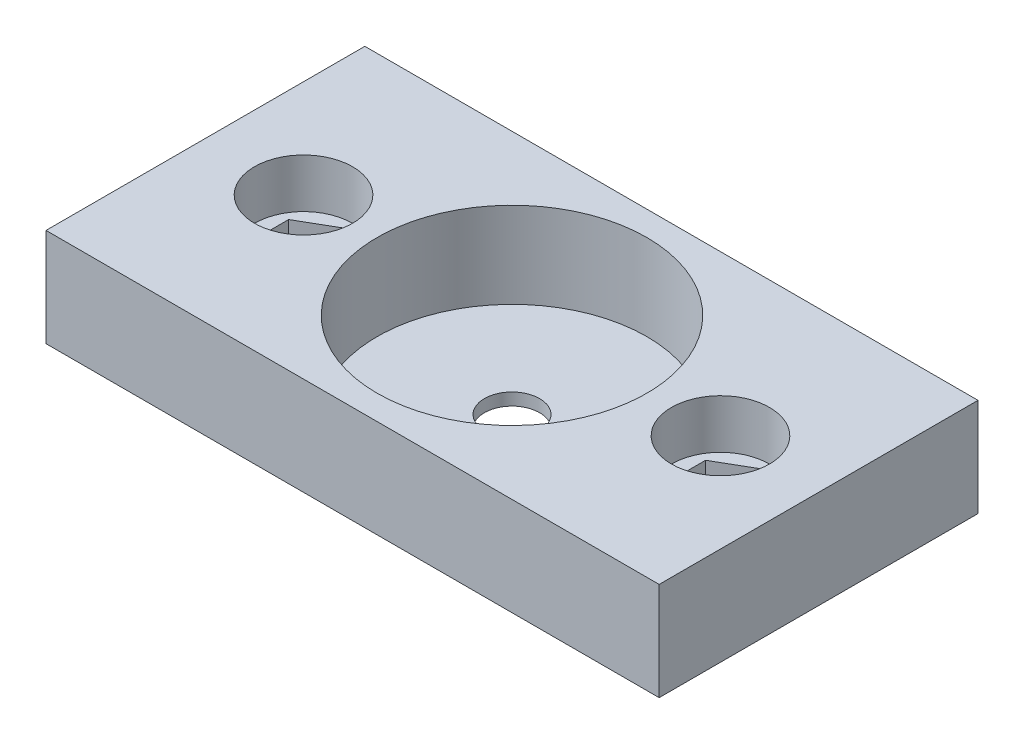
SolidWorks part; units mm, degrees
ref_plane "Front Plane" through (0, 0, 0) normal (0, 0, 1) x (1, 0, 0)
ref_plane "Top Plane" through (0, 0, 0) normal (0, 1, 0) x (1, 0, 0)
ref_plane "Right Plane" through (0, 0, 0) normal (1, 0, 0) x (0, 0, -1)
sketch "Sketch1" plane through (0, 0, 0) normal (0, 1, 0) x (1, 0, 0)
  line L1 (-25, 13) -> (25, 13)
  line L2 (-25, 13) -> (-25, -13)
  line L3 (-25, -13) -> (25, -13)
  line L4 (25, 13) -> (25, -13)
  line L5 (0, -13) -> (0, 13) construction
  line L6 (-25, 0) -> (25, 0) construction
  point P4 (0, 0)
  point P284 (0, 0)
  dimension "D1" = 50
  dimension "D2" = 26
extrude "Boss-Extrude1" add sketch "Sketch1" along normal blind 8
ref_plane "end_stop" through (25, 0, 0) normal (1, 0, 0) x (0, 0, -1)
sketch "Sketch2" plane through (0, 8, 0) normal (0, 1, 0) x (1, 0, 0)
  line L4 (-4.4, 0) -> (4.4, 0) construction
  line L5 (0, -4.4) -> (0, 4.4) construction
  circle A1 centre (0, 0) radius 11
  point P1 (0, 0)
  point P2 (0, 0)
  point P6 (0, 0)
  point P7 (0, 0)
  dimension "D2" = 22
extrude "Cut-Extrude1" cut sketch "Sketch2" against normal offset from surface (7 mm away) 1 up to face at (0, 0, 0)
sketch "Sketch5" plane through (0, 1, 0) normal (0, 1, 0) x (1, 0, 0)
  circle A0 centre (0, 0) radius 2.25
  dimension "D1" = 4.5
extrude "Cut-Extrude2" cut sketch "Sketch5" against normal through all
sketch "Sketch6" plane through (0, 8, 0) normal (0, 1, 0) x (1, 0, 0)
  line L0 (-4.4, 0) -> (4.4, 0) construction
  line L2 (0, -4.4) -> (0, 4.4) construction
  circle A0 centre (17, 0) radius 4
  circle A3 centre (-17, 0) radius 4
  point P2 (0, 0)
  point P4 (0, 0)
  point P5 (0, 0)
  point P8 (0, 0)
  point P9 (0, 0)
  point P12 (0, 0)
  dimension "D1" = 8
  dimension "D2" = 17
extrude "Cut-Extrude3" cut sketch "Sketch6" against normal blind 4
sketch "Sketch7" plane through (0, 4, 0) normal (0, 1, 0) x (1, 0, 0)
  line L0 (25, -4.4) -> (25, 4.4) construction
  line L1 (19.875, -1.6599) -> (19.875, 1.6599)
  line L2 (19.875, 1.6599) -> (17, 3.3198)
  line L3 (17, 3.3198) -> (14.125, 1.6599)
  line L4 (14.125, 1.6599) -> (14.125, -1.6599)
  line L5 (14.125, -1.6599) -> (17, -3.3198)
  line L6 (17, -3.3198) -> (19.875, -1.6599)
  line L13 (0, -4.4) -> (0, 4.4) construction
  line L14 (-17, -3.3198) -> (-19.875, -1.6599)
  line L15 (-14.125, -1.6599) -> (-17, -3.3198)
  line L16 (-14.125, 1.6599) -> (-14.125, -1.6599)
  line L17 (-17, 3.3198) -> (-14.125, 1.6599)
  line L18 (-19.875, 1.6599) -> (-17, 3.3198)
  line L19 (-19.875, -1.6599) -> (-19.875, 1.6599)
  circle A0 centre (17, 0) radius 2.875 construction
  circle A1 centre (-17, 0) radius 2.875 construction
  point P19 (53, 0)
  point P20 (53, 0)
  point P21 (53, 0)
  dimension "D1" = 5.75
extrude "Cut-Extrude4" cut sketch "Sketch7" against normal blind 2.2
hole_wizard "M3 Clearance Hole1" positions "Sketch8" profile "Sketch9" hole size "M3" standard "ISO" end condition up to next
sketch "Sketch8" plane through (0, 1.8, 0) normal (0, 1, 0) x (1, 0, 0)
  line L0 (0, -4.4) -> (0, 4.4) construction
  point P17 (17, 0)
  point P23 (-17, 0)
sketch "Sketch9" plane through (17, 1.8, 0) normal (1, 0, 0) x (0, 0, 1)
  line L0 (0, 0) -> (0, 1.8)
  line L1 (0, 1.8) -> (1.7, 1.8)
  line L2 (1.7, 1.8) -> (1.7, 0)
  line L5 (1.7, 0) -> (0, 0)
  line L11 (0, -6.35) -> (0, 107.95) construction
  dimension "Thru Hole Dia." = 3.4
  dimension "Thru Hole Depth" = 1.8
